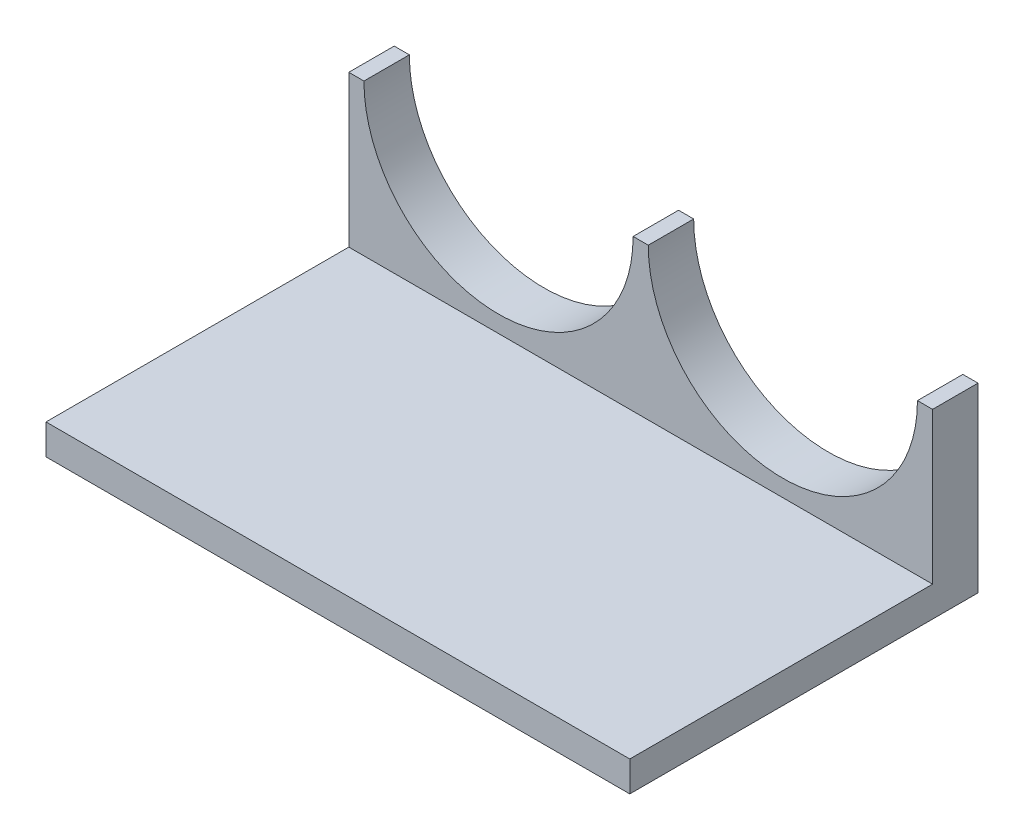
SolidWorks part; units mm, degrees
ref_plane "Front Plane" through (0, 0, 0) normal (0, 0, 1) x (1, 0, 0)
ref_plane "Top Plane" through (0, 0, 0) normal (0, 1, 0) x (1, 0, 0)
ref_plane "Right Plane" through (0, 0, 0) normal (1, 0, 0) x (0, 0, -1)
sketch "Sketch7" plane through (0, 0, 0) normal (0, 0, 1) x (1, 0, 0)
  line L0 (0, 10) -> (0, 60)
  line L1 (93.9, 60) -> (98.9, 60)
  line L2 (93.9, 60) -> (5, 60) construction
  line L3 (0, 60) -> (5, 60)
  line L4 (187.8, 60) -> (98.9, 60) construction
  line L5 (187.8, 60) -> (192.8, 60)
  line L6 (192.8, 60) -> (192.8, 0)
  line L7 (0, 10) -> (0, 0)
  line L8 (0, 0) -> (192.8, 0)
  arc A0 (5, 60) -> (93.9, 60) centre (49.45, 60) ccw
  arc A1 (98.9, 60) -> (187.8, 60) centre (143.35, 60) ccw
  point P7 (0, 10)
  dimension "D1" = 88.9
  dimension "D2" = 10
  dimension "5" = 5
  dimension "D3" = 50
extrude "Boss-Extrude2" add sketch "Sketch7" along normal blind 15
sketch "Sketch8" plane through (0, 0, 15) normal (0, 0, 1) x (1, 0, 0)
  line L0 (192.8, 0) -> (192.8, 60) construction
  line L1 (0, 0) -> (192.8, 0)
  line L2 (0, 0) -> (0, 10)
  line L3 (0, 10) -> (192.8, 10)
  line L4 (192.8, 0) -> (192.8, 10)
  dimension "D1" = 10
extrude "Boss-Extrude3" add sketch "Sketch8" along normal blind 100
